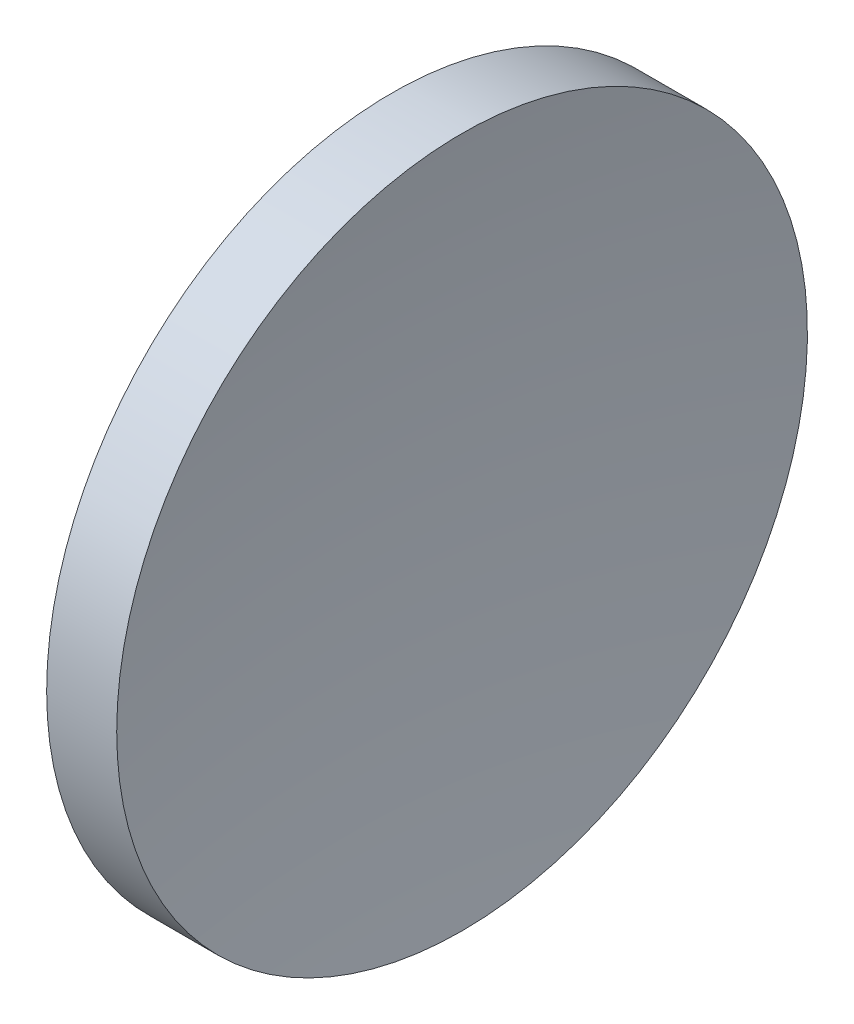
SolidWorks part; units mm, degrees
ref_plane "前视基准面" through (0, 0, 0) normal (0, 0, 1) x (1, 0, 0)
ref_plane "上视基准面" through (0, 0, 0) normal (0, 1, 0) x (1, 0, 0)
ref_plane "右视基准面" through (0, 0, 0) normal (1, 0, 0) x (0, 0, -1)
sketch "草图1" plane through (0, 0, 0) normal (0, 0, 1) x (1, 0, 0)
  line L0 (105.6218, 65.1556) -> (137.1869, 65.1556) construction
  line L1 (113.9119, 65.1556) -> (113.9119, 85.1556)
  line L2 (116.4119, 65.1556) -> (113.9119, 65.1556)
  line L3 (113.9119, 85.1556) -> (117.9688, 85.1556)
  arc A0 (117.9688, 85.1556) -> (116.4119, 65.1556) centre (245.6519, 65.1556) ccw
revolve "旋转1" add sketch "草图1" angle 360 about L0
